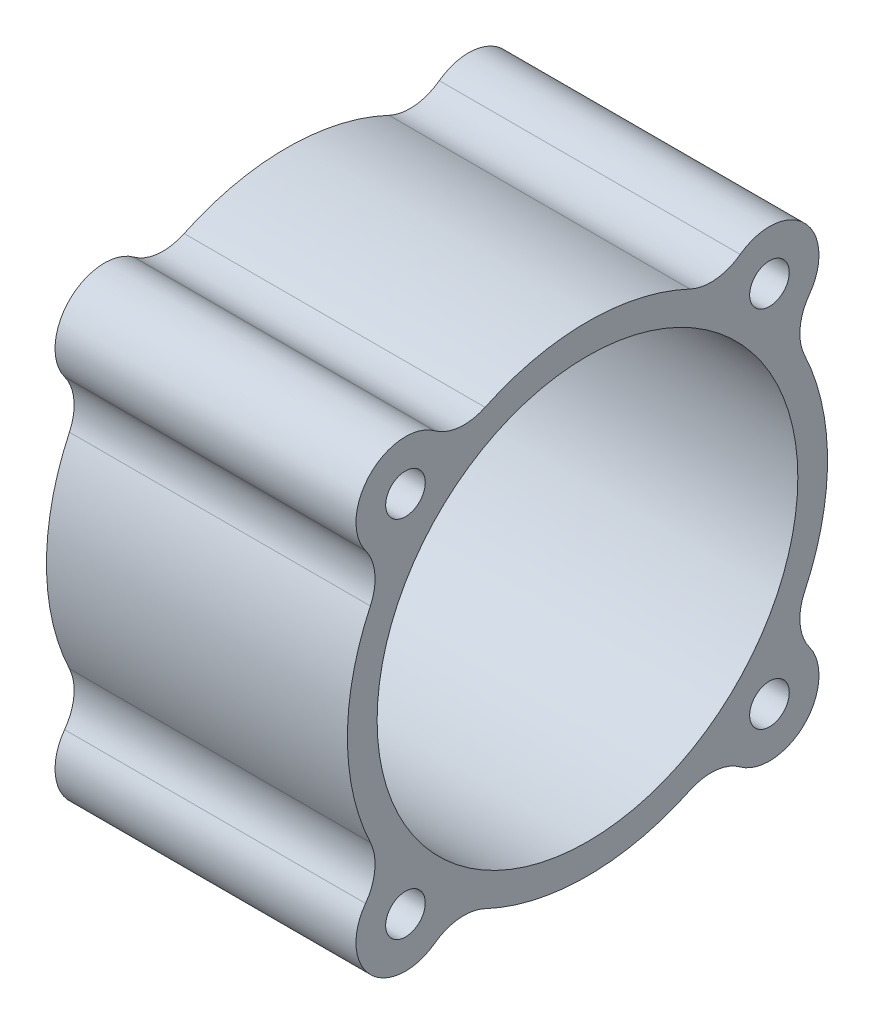
SolidWorks part; units mm, degrees
material "聚脂树脂"
ref_plane "前视基准面" through (0, 0, 0) normal (0, 0, 1) x (1, 0, 0)
ref_plane "上视基准面" through (0, 0, 0) normal (0, 1, 0) x (1, 0, 0)
ref_plane "右视基准面" through (0, 0, 0) normal (1, 0, 0) x (0, 0, -1)
sketch "草图1" plane through (0, 0, 0) normal (1, 0, 0) x (0, 0, -1)
  circle A0 centre (0, 0) radius 21.25
  circle A2 centre (-18.3848, 18.3848) radius 2
  arc A3 (-15.4318, 22.4196) -> (-22.4196, 15.4318) centre (-18.3848, 18.3848) ccw
  arc A4 (-15.4318, 22.4196) -> (-10.3457, 21.9324) centre (-12.4789, 26.4545) ccw
  arc A5 (-22.4196, 15.4318) -> (-21.9324, 10.3457) centre (-26.4545, 12.4789) cw
  circle A6 centre (18.3848, 18.3848) radius 2
  arc A9 (22.4196, 15.4318) -> (15.4318, 22.4196) centre (18.3848, 18.3848) ccw
  arc A10 (22.4196, 15.4318) -> (21.9324, 10.3457) centre (26.4545, 12.4789) ccw
  arc A13 (15.4318, 22.4196) -> (10.3457, 21.9324) centre (12.4789, 26.4545) cw
  arc A14 (21.9324, -10.3457) -> (21.9324, 10.3457) centre (0, 0) ccw
  circle A17 centre (18.3848, -18.3848) radius 2
  arc A18 (10.3457, 21.9324) -> (-10.3457, 21.9324) centre (0, 0) ccw
  arc A19 (15.4318, -22.4196) -> (22.4196, -15.4318) centre (18.3848, -18.3848) ccw
  arc A20 (15.4318, -22.4196) -> (10.3457, -21.9324) centre (12.4789, -26.4545) ccw
  arc A21 (22.4196, -15.4318) -> (21.9324, -10.3457) centre (26.4545, -12.4789) cw
  arc A22 (-10.3457, -21.9324) -> (10.3457, -21.9324) centre (0, 0) ccw
  circle A23 centre (-18.3848, -18.3848) radius 2
  arc A24 (-22.4196, -15.4318) -> (-15.4318, -22.4196) centre (-18.3848, -18.3848) ccw
  arc A25 (-22.4196, -15.4318) -> (-21.9324, -10.3457) centre (-26.4545, -12.4789) ccw
  arc A26 (-15.4318, -22.4196) -> (-10.3457, -21.9324) centre (-12.4789, -26.4545) cw
  arc A27 (-21.9324, 10.3457) -> (-21.9324, -10.3457) centre (0, 0) ccw
  circle A28 centre (0, 0) radius 26 construction
  dimension "D1" = 4
  dimension "D2" = 42.5
  dimension "D3" = 52
  dimension "D4" = 4
  dimension "D5" = 5
  dimension "D6" = 3
  dimension "D7" = 5
extrude "凸台-拉伸1" add sketch "草图1" along normal mid plane 30.4
